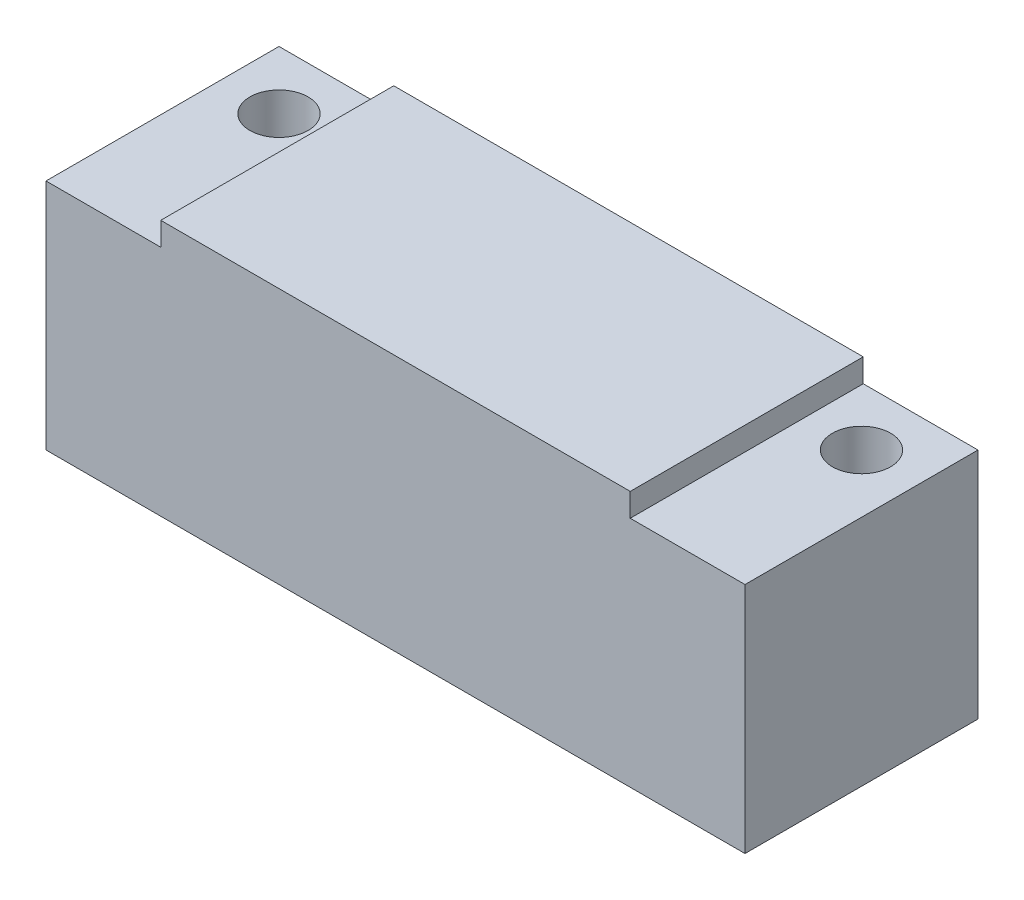
SolidWorks part; units mm, degrees
ref_plane "Front Plane" through (0, 0, 0) normal (0, 0, 1) x (1, 0, 0)
ref_plane "Top Plane" through (0, 0, 0) normal (0, 1, 0) x (1, 0, 0)
ref_plane "Right Plane" through (0, 0, 0) normal (1, 0, 0) x (0, 0, -1)
sketch "Sketch1" plane through (0, 0, 0) normal (0, 0, 1) x (1, 0, 0)
  line L1 (0, 0) -> (60, 0)
  line L2 (0, 0) -> (0, 20)
  line L3 (9.85, 22) -> (50.15, 22)
  line L4 (60, 0) -> (60, 20)
  line L7 (0, 20) -> (9.85, 20)
  line L8 (9.85, 22) -> (9.85, 20)
  line L11 (60, 20) -> (50.15, 20)
  line L12 (50.15, 22) -> (50.15, 20)
  point P1 (30, 22)
  point P2 (30, 0)
  dimension "D1" = 60
  dimension "D2" = 40.3
  dimension "D3" = 2
  dimension "D4" = 20
extrude "Boss-Extrude1" add sketch "Sketch1" along normal blind 20
sketch "Sketch2" plane through (0, 0, 0) normal (0, -1, 0) x (1, 0, 0)
  line L0 (60, 20) -> (60, 0) construction
  line L1 (0, 20) -> (0, 0) construction
  line L2 (0, 0) -> (60, 0) construction
  circle A0 centre (55, 5) radius 2.5
  circle A1 centre (5, 5) radius 2.5
  dimension "D1" = 5
  dimension "D2" = 5
  dimension "D3" = 5
  dimension "D4" = 5
extrude "Cut-Extrude1" cut sketch "Sketch2" against normal through all
